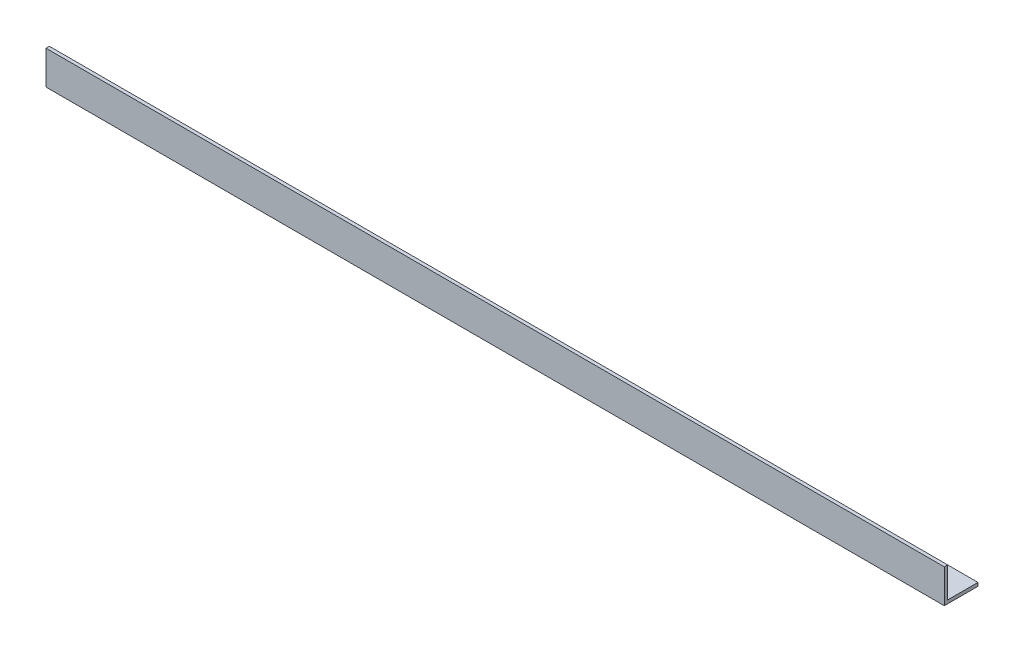
SolidWorks part; units mm, degrees
ref_plane "Спереди" through (0, 0, 0) normal (0, 0, 1) x (1, 0, 0)
ref_plane "Сверху" through (0, 0, 0) normal (0, 1, 0) x (1, 0, 0)
ref_plane "Справа" through (0, 0, 0) normal (1, 0, 0) x (0, 0, -1)
sketch "Эскиз1" plane through (0, 0, 0) normal (1, 0, 0) x (0, 0, -1)
  line L0 (0, 0) -> (0, 15)
  line L1 (0, 15) -> (1.5, 15)
  line L2 (1.5, 15) -> (1.5, 1.5)
  line L3 (1.5, 1.5) -> (15, 1.5)
  line L4 (15, 1.5) -> (15, 0)
  line L5 (15, 0) -> (0, 0)
  dimension "D1" = 15
  dimension "D2" = 15
  dimension "D3" = 1.5
  dimension "D4" = 1.5
extrude "Бобышка-Вытянуть1" add sketch "Эскиз1" along normal blind 400
